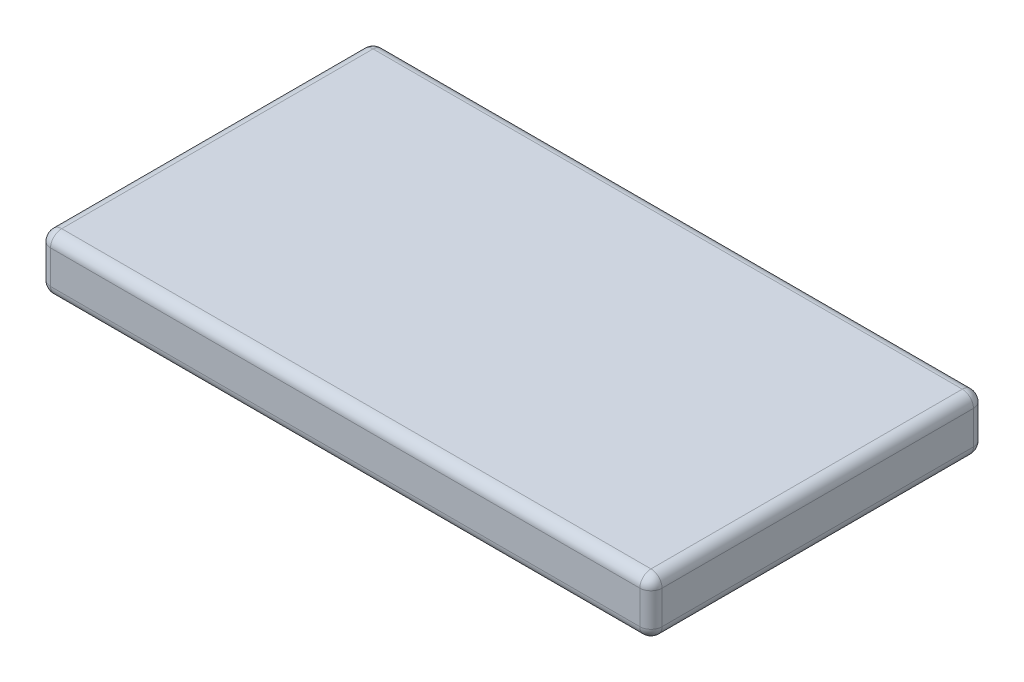
SolidWorks part; units mm, degrees
ref_plane "Front Plane" through (0, 0, 0) normal (0, 0, 1) x (1, 0, 0)
ref_plane "Top Plane" through (0, 0, 0) normal (0, 1, 0) x (1, 0, 0)
ref_plane "Right Plane" through (0, 0, 0) normal (1, 0, 0) x (0, 0, -1)
sketch "Sketch1" plane through (0, 0, 0) normal (0, 1, 0) x (1, 0, 0)
  line L1 (-27.5, 15) -> (27.5, 15)
  line L2 (-27.5, 15) -> (-27.5, -15)
  line L3 (-27.5, -15) -> (27.5, -15)
  line L4 (27.5, 15) -> (27.5, -15)
  line L5 (-27.5, 15) -> (27.5, -15) construction
  line L6 (-27.5, -15) -> (27.5, 15) construction
  point P0 (0, 0)
  dimension "D1" = 30
  dimension "D2" = 55
extrude "Shape" add sketch "Sketch1" along normal blind 5
fillet "Fillets" radius 1 12 edges at (-27.5, 0, 0) (-27.5, 2.5, -15) (0, 0, -15) (27.5, 2.5, -15) (27.5, 0, 0) (-27.5, 2.5, 15) (27.5, 2.5, 15) (0, 0, 15) (0, 5, 15) (-27.5, 5, 0) (0, 5, -15) (27.5, 5, 0)
